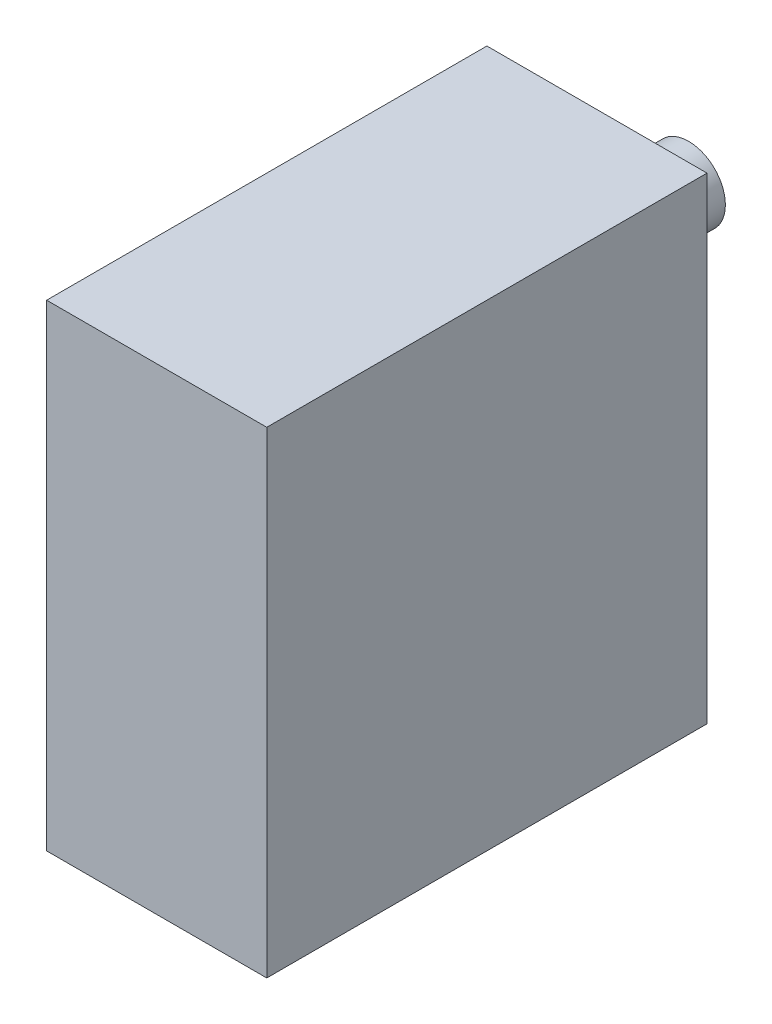
SolidWorks part; units mm, degrees
ref_plane "Front Plane" through (0, 0, 0) normal (0, 0, 1) x (1, 0, 0)
ref_plane "Top Plane" through (0, 0, 0) normal (0, 1, 0) x (1, 0, 0)
ref_plane "Right Plane" through (0, 0, 0) normal (1, 0, 0) x (0, 0, -1)
sketch "Sketch1" plane through (0, 0, 0) normal (0, 0, 1) x (1, 0, 0)
  line L1 (-9.525, 20.6375) -> (9.525, 20.6375)
  line L2 (-9.525, 20.6375) -> (-9.525, -20.6375)
  line L3 (-9.525, -20.6375) -> (9.525, -20.6375)
  line L4 (9.525, 20.6375) -> (9.525, -20.6375)
  line L5 (-9.525, 20.6375) -> (9.525, -20.6375) construction
  line L6 (-9.525, -20.6375) -> (9.525, 20.6375) construction
  point P0 (0, 0)
  dimension "D1" = 41.275
  dimension "D2" = 19.05
extrude "Boss-Extrude1" add sketch "Sketch1" along normal blind 38.1
sketch "Sketch6" plane through (0, 0, 0) normal (0, 0, -1) x (-1, 0, 0)
  line L0 (-9.525, 20.6375) -> (9.525, 20.6375) construction
  circle A0 centre (0, 11.1125) radius 3.175
  dimension "D1" = 9.525
  dimension "D2" = 6.35
extrude "Boss-Extrude4" add sketch "Sketch6" along normal blind 7.9375
